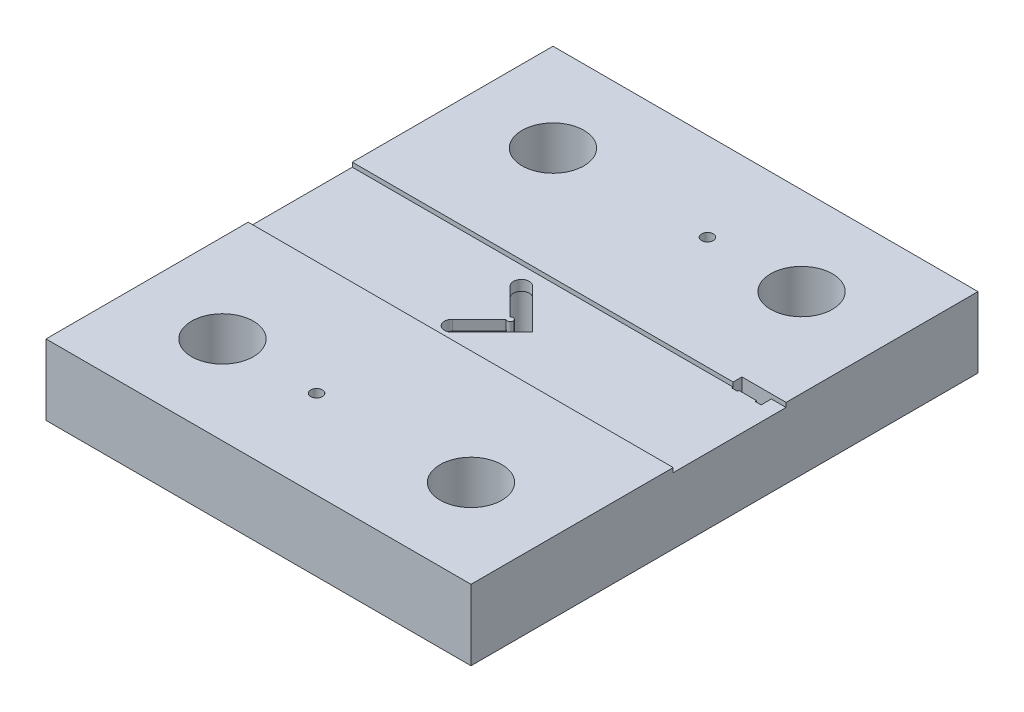
SolidWorks part; units mm, degrees
ref_plane "Front Plane" through (0, 0, 0) normal (0, 0, 1) x (1, 0, 0)
ref_plane "Top Plane" through (0, 0, 0) normal (0, 1, 0) x (1, 0, 0)
ref_plane "Right Plane" through (0, 0, 0) normal (1, 0, 0) x (0, 0, -1)
sketch "Sketch2" plane through (0, 0, 0) normal (0, 1, 0) x (1, 0, 0)
  line L1 (-72.25, -86.19) -> (72.25, -86.19)
  line L2 (-72.25, -86.19) -> (-72.25, 86.19)
  line L3 (-72.25, 86.19) -> (72.25, 86.19)
  line L4 (72.25, -86.19) -> (72.25, 86.19)
  line L5 (-72.25, -86.19) -> (72.25, 86.19) construction
  line L6 (-72.25, 86.19) -> (72.25, -86.19) construction
  point P0 (0, 0)
  dimension "D1" = 144.5
  dimension "D2" = 172.38
extrude "Boss-Extrude1" add sketch "Sketch2" along normal blind 24
sketch "Sketch3" plane through (0, 24, 0) normal (0, 1, 0) x (1, 0, 0)
  line L0 (-72.25, 86.19) -> (-72.25, -86.19) construction
  line L1 (-72.25, -17.44) -> (72.25, -17.44) construction
  line L2 (-72.25, -17.44) -> (-72.25, 17.94) construction
  line L3 (-72.25, 17.94) -> (57.25, 17.94) construction
  line L4 (72.25, -17.44) -> (72.25, 32.6497) construction
  line L5 (72.25, -86.19) -> (72.25, 86.19) construction
  line L6 (62.25, 17.94) -> (62.25, 36.5993) construction
  line L8 (57.25, 17.94) -> (57.25, 20.94) construction
  line L9 (57.25, 20.94) -> (72.25, 20.94) construction
  line L10 (72.25, 32.6497) -> (72.25, 20.94) construction
  line L11 (57.25, 17.44) -> (59.25, 17.44)
  line L12 (57.25, 17.44) -> (57.25, 20.94)
  line L13 (57.25, 20.94) -> (67.25, 20.94)
  line L14 (67.25, 17.44) -> (67.25, 20.94)
  line L16 (59.25, 17.44) -> (59.25, 17.94)
  line L17 (59.25, 17.94) -> (65.25, 17.94)
  line L18 (65.25, 17.44) -> (65.25, 17.94)
  line L19 (65.25, 17.44) -> (67.25, 17.44)
  line L20 (0, 0) -> (42.8345, 0) construction
  line L21 (-10.4555, 9.8288) -> (-1.3339, 0.7071)
  line L22 (-1.3339, -0.7071) -> (-10.4555, -9.8288)
  line L23 (-6.6372, 13.6472) -> (7.01, 0)
  line L24 (7.01, 0) -> (-6.6372, -13.6472)
  line L25 (72.25, 86.19) -> (-72.25, 86.19) construction
  line L26 (-10.4555, 9.8288) -> (-0.6268, 0) construction
  line L27 (-0.6268, 0) -> (-10.4555, -9.8288) construction
  line L28 (0, 0) -> (0, 3.3961) construction
  line L29 (0, 0) -> (-3.75, 0) construction
  line L30 (-72.25, -86.19) -> (72.25, -86.19) construction
  arc A0 (-10.4555, 9.8288) -> (-6.6372, 13.6472) centre (-8.5463, 11.738) cw
  arc A1 (-10.4555, -9.8288) -> (-6.6372, -13.6472) centre (-8.5463, -11.738) ccw
  arc A2 (-1.3339, -0.7071) -> (-1.3339, 0.7071) centre (-0.6268, 0) ccw
  circle A3 centre (42.25, 56.19) radius 10.5
  circle A4 centre (-42.25, 56.19) radius 10.5
  circle A5 centre (-42.25, -56.19) radius 10.5
  circle A6 centre (42.25, -56.19) radius 10.5
  circle A7 centre (10.25, 56.19) radius 1.99
  circle A8 centre (-10.25, -56.19) radius 1.99
  dimension "D8" = 19.3
  dimension "D13" = 30
  dimension "D19" = 3.98
  dimension "D20" = 3.98
  dimension "D1" = 6
  dimension "D2" = 0.5
  dimension "D3" = 3.5
  dimension "D4" = 0.5
  dimension "D5" = 10
  dimension "D6" = 15
  dimension "D9" = 19.3
  dimension "D10" = 17.94
  dimension "D11" = 17.44
  dimension "D12" = 50.24
  dimension "D14" = 30
  dimension "D15" = 62
  dimension "D16" = 62
  dimension "D17" = 30
  dimension "D18" = 30
  dimension "D7" = 5.4
extrude "Cut-Extrude2" cut sketch "Sketch3" against normal through all
sketch "Sketch5" plane through (0, 24, 0) normal (0, 1, 0) x (1, 0, 0)
  line L0 (-72.25, 17.94) -> (57.25, 17.94) construction
  line L1 (-72.25, -17.44) -> (-72.25, 17.94) construction
  line L2 (-72.25, -17.44) -> (72.25, -17.44) construction
  line L3 (72.25, -17.44) -> (72.25, 32.6497) construction
  line L4 (72.25, 32.6497) -> (72.25, 20.94) construction
  line L5 (57.25, 20.94) -> (72.25, 20.94) construction
  line L6 (57.25, 17.94) -> (57.25, 20.94) construction
  line L7 (-72.25, 17.94) -> (57.25, 17.94)
  line L8 (-72.25, -17.44) -> (-72.25, 17.94)
  line L9 (-72.25, -17.44) -> (72.25, -17.44)
  line L10 (72.25, -17.44) -> (72.25, 32.6497)
  line L11 (72.25, 32.6497) -> (72.25, 20.94)
  line L12 (57.25, 20.94) -> (72.25, 20.94)
  line L13 (57.25, 17.94) -> (57.25, 20.94)
  line M1 (57.25, 17.44) -> (57.25, 20.94)
  line M3 (67.25, 20.94) -> (67.25, 17.44)
  line M4 (67.25, 17.44) -> (65.25, 17.44)
  line M5 (65.25, 17.44) -> (65.25, 17.94)
  line M6 (65.25, 17.94) -> (59.25, 17.94)
  line M7 (59.25, 17.94) -> (59.25, 17.44)
  line M8 (59.25, 17.44) -> (57.25, 17.44)
  line M15 (-1.3339, 0.7071) -> (-10.4555, 9.8288)
  arc M16 (-10.4555, 9.8288) -> (-6.6372, 13.6472) centre (-8.5463, 11.738) cw
  line M17 (-6.6372, 13.6472) -> (7.01, 0)
  line M18 (7.01, 0) -> (-6.6372, -13.6472)
  arc M19 (-6.6372, -13.6472) -> (-10.4555, -9.8288) centre (-8.5463, -11.738) cw
  line M20 (-10.4555, -9.8288) -> (-1.3339, -0.7071)
  arc M21 (-1.3339, -0.7071) -> (-1.3339, 0.7071) centre (-0.6268, 0) ccw
  line M22 (72.25, -86.19) -> (72.25, 86.19)
  line M24 (-72.25, 86.19) -> (-72.25, -86.19)
extrude "Cut-Extrude3" cut sketch "Sketch5" against normal blind 1.5 contours L12 L7 L9 M3 M4 M5 M6 M7 M8 M1 M24 M22 M21 M15 M16 M17 M18 M19 M20
sketch "Sketch7" plane through (0, 0, 0) normal (0, -1, 0) x (1, 0, 0)
  line L9 (-2.041, 0) -> (-11.1626, -9.1217)
  line L10 (-11.1626, 9.1217) -> (-2.041, 0)
  line L11 (8.4242, 0) -> (-5.9301, 14.3543)
  line L12 (-5.9301, -14.3543) -> (8.4242, 0)
  line L13 (-2.041, 0) -> (-11.1626, -9.1217)
  line L14 (-11.1626, 9.1217) -> (-2.041, 0)
  line L15 (8.4242, 0) -> (-5.9301, 14.3543)
  line L16 (-5.9301, -14.3543) -> (8.4242, 0)
  arc A6 (-11.1626, -9.1217) -> (-5.9301, -14.3543) centre (-8.5463, -11.738) ccw
  arc A7 (-5.9301, 14.3543) -> (-11.1626, 9.1217) centre (-8.5463, 11.738) ccw
  arc A8 (-11.1626, -9.1217) -> (-5.9301, -14.3543) centre (-8.5463, -11.738) ccw
  arc A9 (-5.9301, 14.3543) -> (-11.1626, 9.1217) centre (-8.5463, 11.738) ccw
  dimension "D1" = 1
extrude "Cut-Extrude4" cut sketch "Sketch7" against normal blind 19
